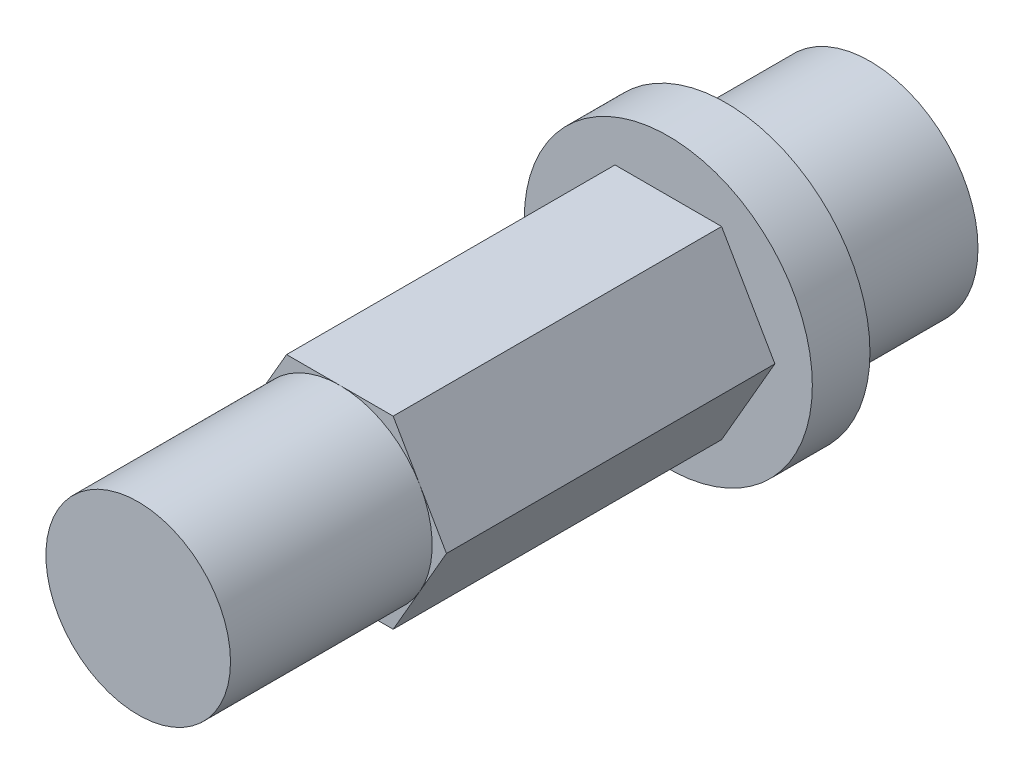
SolidWorks part; units mm, degrees
ref_plane "Front Plane" through (0, 0, 0) normal (0, 0, 1) x (1, 0, 0)
ref_plane "Top Plane" through (0, 0, 0) normal (0, 1, 0) x (1, 0, 0)
ref_plane "Right Plane" through (0, 0, 0) normal (1, 0, 0) x (0, 0, -1)
sketch "Sketch1" plane through (0, 0, 0) normal (0, 0, 1) x (1, 0, 0)
  circle A0 centre (0, 0) radius 3.75
  dimension "D1" = 7.5
extrude "Boss-Extrude1" add sketch "Sketch1" along normal blind 5
sketch "Sketch2" plane through (0, 0, 5) normal (0, 0, 1) x (1, 0, 0)
  circle A0 centre (0, 0) radius 5
  dimension "D1" = 10
extrude "Boss-Extrude2" add sketch "Sketch2" along normal blind 2
sketch "Sketch3" plane through (0, 0, 7) normal (0, 0, 1) x (1, 0, 0)
  line L7 (3.7, 0) -> (1.85, 3.2043)
  line L8 (1.85, 3.2043) -> (-1.85, 3.2043)
  line L9 (-1.85, 3.2043) -> (-3.7, 0)
  line L10 (-3.7, 0) -> (-1.85, -3.2043)
  line L11 (-1.85, -3.2043) -> (1.85, -3.2043)
  line L12 (1.85, -3.2043) -> (3.7, 0)
  circle A0 centre (0, 0) radius 3.7 construction
  circle A1 centre (0, 0) radius 3.2043 construction
  point P1 (3.75, 0)
  dimension "D1" = 7.4
extrude "Boss-Extrude3" add sketch "Sketch3" along normal blind 11.4
sketch "Sketch4" plane through (0, 0, 18.4) normal (0, 0, 1) x (1, 0, 0)
  line L2 (-1.85, 3.2043) -> (-3.7, 0) construction
  circle A0 centre (0, 0) radius 3.2043
extrude "Boss-Extrude4" add sketch "Sketch4" along normal blind 7
